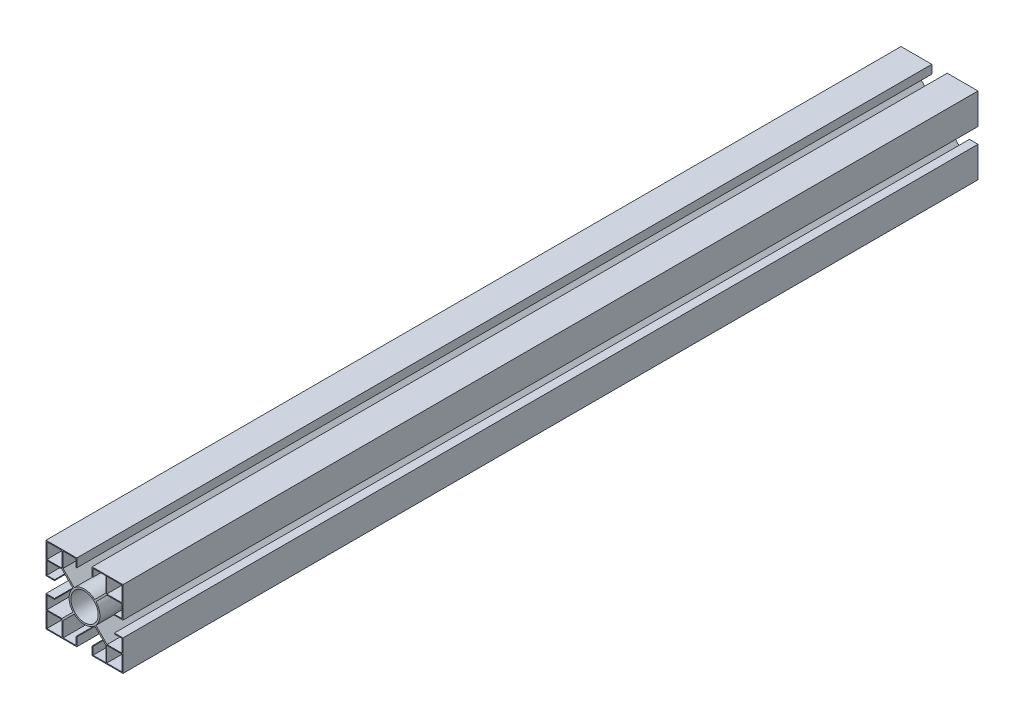
SolidWorks part; units mm, degrees
material "201.0-T7 Molde de fundição com isolamento (SS)"
ref_plane "Plano frontal" through (0, 0, 0) normal (0, 0, 1) x (1, 0, 0)
ref_plane "Plano superior" through (0, 0, 0) normal (0, 1, 0) x (1, 0, 0)
ref_plane "Plano direito" through (0, 0, 0) normal (1, 0, 0) x (0, 0, -1)
sketch "Esboço1" plane through (0, 0, 0) normal (0, 0, 1) x (1, 0, 0)
  line L1 (-6.0006, -6.7077) -> (-12.5, -13.2071)
  line L2 (22.5, -22.5) -> (22.5, -4.5)
  line L3 (22.5, 22.5) -> (4.5, 22.5)
  line L4 (-22.5, -22.5) -> (-22.5, -4.5)
  line L5 (-5, -22) -> (-5, -17.5)
  line L6 (-5, -22) -> (-22, -22)
  line L7 (-22.5, 22.5) -> (-12.5, 22.5)
  line L8 (-22.5, 22.5) -> (-22.5, 12.5)
  line L9 (-22, 12.5) -> (-13.2071, 12.5)
  line L10 (-12.5, 22) -> (-12.5, 13.2071)
  line L11 (22.5, 22.5) -> (12.5, 22.5)
  line L12 (22.5, 22.5) -> (22.5, 12.5)
  line L13 (22.5, 12.5) -> (13.2071, 12.5)
  line L14 (12.5, 22.5) -> (12.5, 13.2071)
  line L15 (-22, -22) -> (-22, -5)
  line L16 (-22, -5) -> (-17.5, -5)
  line L17 (-22, 22) -> (-22, 13)
  line L18 (6.7077, 6.0006) -> (13.2071, 12.5)
  line L19 (6.0006, 6.7077) -> (12.5, 13.2071)
  line L20 (-6.7077, 6.0006) -> (-13.2071, 12.5)
  line L21 (-22, 13) -> (-13, 13)
  line L22 (-17.5, -5) -> (-17.5, -4.5)
  line L23 (-13, 22) -> (-13, 13)
  line L24 (-22.5, 12.5) -> (-12.5, 12.5) construction
  line L25 (-22, 22) -> (-13, 22)
  line L26 (22, 22) -> (13, 22)
  line L27 (13, 22) -> (13, 13)
  line L28 (22, 13) -> (13, 13)
  line L29 (22, 22) -> (22, 13)
  line L30 (-6.0006, 6.7077) -> (-12.5, 13.2071)
  line L31 (-12.5, 22.5) -> (-12.5, 12.5) construction
  line L32 (12.5, 22.5) -> (12.5, 12.5) construction
  line L33 (22.5, 12.5) -> (12.5, 12.5) construction
  line L34 (-6.7077, -6.0006) -> (-13.2071, -12.5)
  line L35 (6.0006, -6.7077) -> (12.5, -13.2071)
  line L36 (6.7077, -6.0006) -> (13.2071, -12.5)
  line L37 (12.5, -22) -> (12.5, -13.2071)
  line L38 (22, -22) -> (13, -22)
  line L39 (13, -22) -> (13, -13)
  line L40 (22, -22) -> (22, -13)
  line L41 (22, -13) -> (13, -13)
  line L42 (22, -12.5) -> (13.2071, -12.5)
  line L43 (-12.5, -22) -> (-12.5, -13.2071)
  line L44 (-13, -22) -> (-13, -13)
  line L45 (-22, -22) -> (-22, -13)
  line L46 (-22, -22) -> (-13, -22)
  line L47 (22.5, -22.5) -> (4.5, -22.5)
  line L48 (-22.5, -12.5) -> (-13.2071, -12.5)
  line L49 (-22, -13) -> (-13, -13)
  line L50 (-4.5, 22.5) -> (-4.5, 17.5)
  line L51 (4.5, 22.5) -> (4.5, 17.5)
  line L52 (-4.5, 22.5) -> (-22.5, 22.5)
  line L53 (-4.5, -22.5) -> (-4.5, -17.5)
  line L54 (4.5, -22.5) -> (4.5, -17.5)
  line L55 (-4.5, -22.5) -> (-22.5, -22.5)
  line L56 (-22.5, 4.5) -> (-17.5, 4.5)
  line L57 (-22.5, -4.5) -> (-17.5, -4.5)
  line L59 (-22.5, 4.5) -> (-22.5, 22.5)
  line L60 (22.5, -4.5) -> (17.5, -4.5)
  line L61 (22.5, 4.5) -> (17.5, 4.5)
  line L62 (22.5, 4.5) -> (22.5, 22.5)
  line L63 (-4.5, -17.5) -> (-5, -17.5)
  line L64 (-5, 22) -> (-5, 17.5)
  line L65 (-5, 22) -> (-22.5, 22)
  line L66 (-22, 5) -> (-22, 22.5)
  line L67 (-22, 5) -> (-17.5, 5)
  line L68 (-5, 17.5) -> (-4.5, 17.5)
  line L69 (-17.5, 4.5) -> (-17.5, 5)
  line L70 (22, -5) -> (17.5, -5)
  line L71 (22, -22) -> (22, -5)
  line L72 (22, -22) -> (5, -22)
  line L73 (5, -22) -> (5, -17.5)
  line L74 (4.5, -17.5) -> (5, -17.5)
  line L75 (17.5, -5) -> (17.5, -4.5)
  line L76 (22.5, 22) -> (5, 22)
  line L77 (5, 22) -> (5, 17.5)
  line L78 (22, 5) -> (17.5, 5)
  line L79 (22, 5) -> (22, 22.5)
  line L80 (4.5, 17.5) -> (5, 17.5)
  line L81 (17.5, 5) -> (17.5, 4.5)
  circle A0 centre (0, 0) radius 8
  arc A1 (6.7077, -6.0006) -> (6.7077, 6.0006) centre (0, 0) ccw
  circle A2 centre (0, 0) radius 9 construction
  arc A3 (6.0006, 6.7077) -> (-6.0006, 6.7077) centre (0, 0) ccw
  arc A4 (-6.7077, 6.0006) -> (-6.7077, -6.0006) centre (0, 0) ccw
  arc A5 (-6.0006, -6.7077) -> (6.0006, -6.7077) centre (0, 0) ccw
  point P0 (0, 0)
  dimension "D9" = 8
  dimension "D1" = 45
  dimension "D2" = 8
  dimension "D3" = 0.5
  dimension "D4" = 0.5
  dimension "D5" = 0.5
  dimension "D10" = 5
  dimension "D11" = 5
  dimension "D12" = 8
  dimension "D13" = 5
  dimension "D14" = 8
  dimension "D15" = 5
  dimension "D6" = 0.5
  dimension "D7" = 0.5
extrude "Ressalto-extrusão4" add sketch "Esboço1" along normal blind 500 contours L1 A5 L35 L37 L72 L39 L41 L71 L42 L36 A1 L18 L13 L79 L28 L27 L76 L14 L19 A3 L30 L10 L65 L23 L21 L66 L9 L20 A4 L34 L48 L15 L49 L44 L6 L43 A0 | L53 L63 L5 L6 L15 L48 L4 L55 | L57 L4 L48 L15 L16 L22 | L78 L81 L61 L62 L13 L79 | L79 L13 L62 L76 L29 | L26 L79 L11 L14 L76 | L79 L76 L12 L3 | L51 L80 L77 L76 L14 L3 | L56 L69 L67 L66 L17 L65 L59 | L64 L68 L50 L52 L66 L25 L65 | L65 L66 L7 L8
